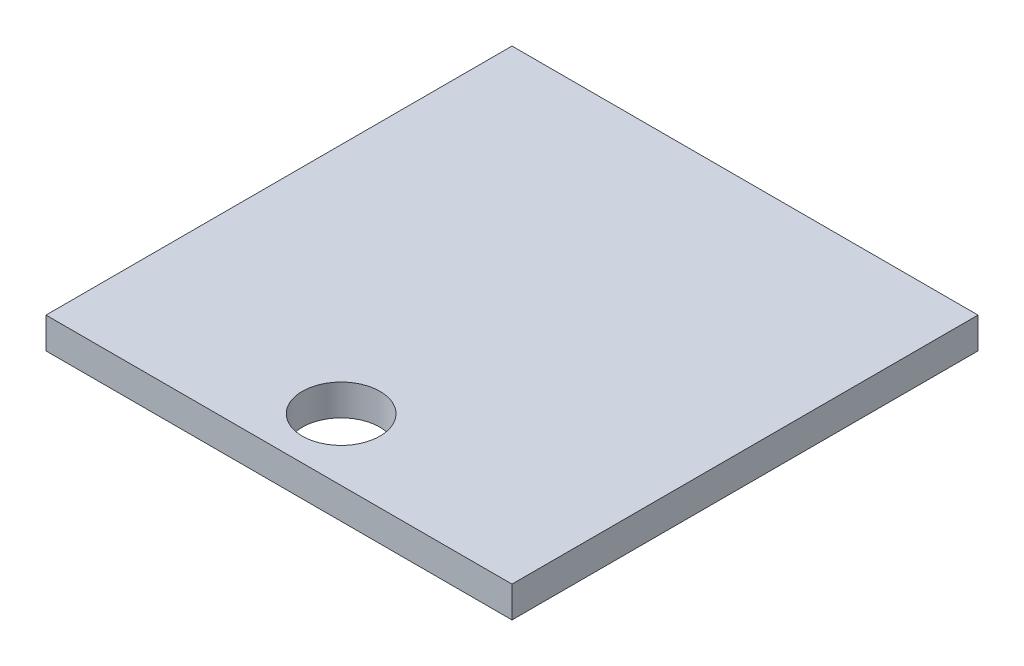
SolidWorks part; units mm, degrees
ref_plane "前视基准面" through (0, 0, 0) normal (0, 0, 1) x (1, 0, 0)
ref_plane "上视基准面" through (0, 0, 0) normal (0, 1, 0) x (1, 0, 0)
ref_plane "右视基准面" through (0, 0, 0) normal (1, 0, 0) x (0, 0, -1)
sketch "草图1" plane through (0, 0, 0) normal (0, 1, 0) x (1, 0, 0)
  line L1 (-7.5, 7.5) -> (7.5, 7.5)
  line L2 (-7.5, 7.5) -> (-7.5, -7.5)
  line L3 (-7.5, -7.5) -> (7.5, -7.5)
  line L4 (7.5, 7.5) -> (7.5, -7.5)
  line L5 (-7.5, 7.5) -> (7.5, -7.5) construction
  line L6 (-7.5, -7.5) -> (7.5, 7.5) construction
  circle A1 centre (0, -5.5) radius 1.25
  point P0 (0, 0)
  dimension "D5" = 2.5
  dimension "D1" = 15
  dimension "D2" = 15
  dimension "D3" = 7.5
  dimension "D4" = 2
extrude "凸台-拉伸1" add sketch "草图1" along normal blind 1
